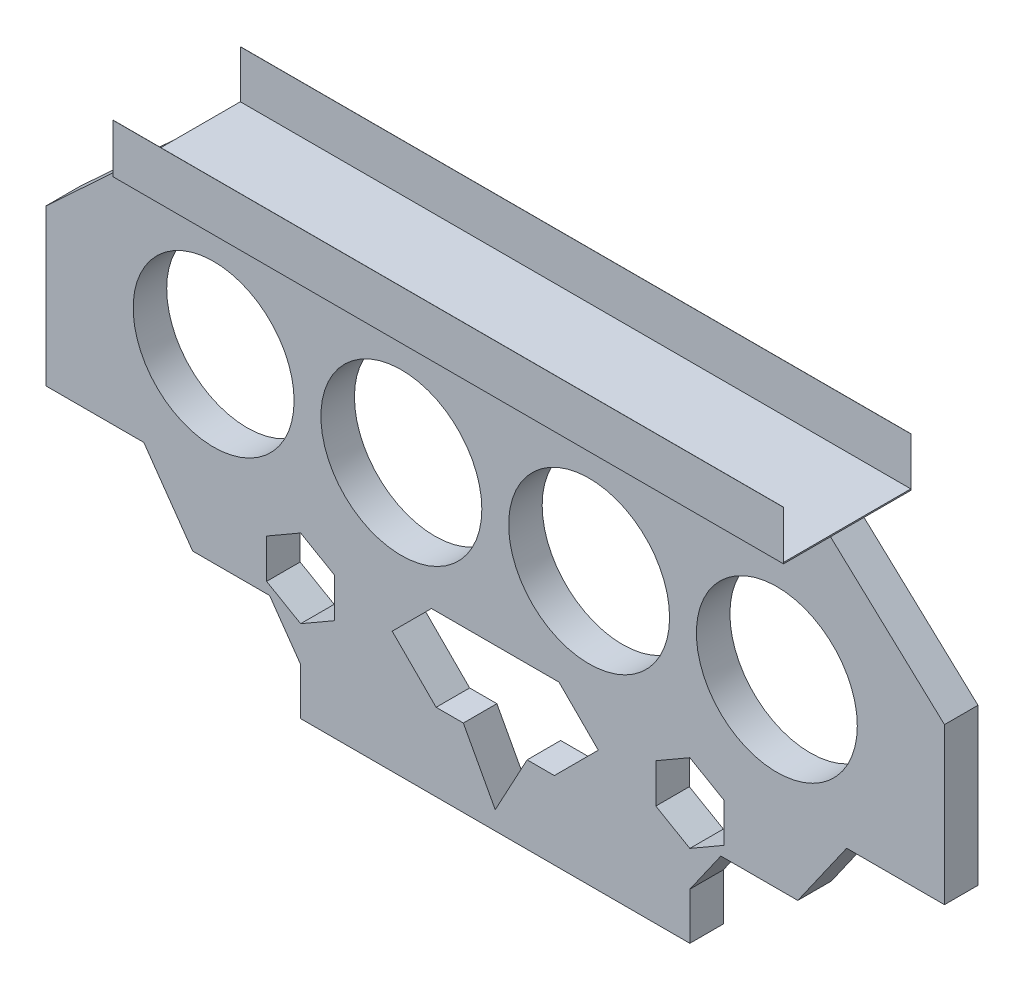
SolidWorks part; units mm, degrees
ref_plane "Front Plane" through (0, 0, 0) normal (0, 0, 1) x (1, 0, 0)
ref_plane "Top Plane" through (0, 0, 0) normal (0, 1, 0) x (1, 0, 0)
ref_plane "Right Plane" through (0, 0, 0) normal (1, 0, 0) x (0, 0, -1)
sketch "Sketch1" plane through (0, 0, 0) normal (0, 0, 1) x (1, 0, 0)
  line L1 (-67, -31.5) -> (67, -31.5)
  line L2 (-67, -31.5) -> (-67, 31.5)
  line L3 (-67, 31.5) -> (67, 31.5)
  line L4 (67, -31.5) -> (67, 31.5)
  line L5 (-67, -31.5) -> (67, 31.5) construction
  line L6 (-67, 31.5) -> (67, -31.5) construction
  point P0 (0, 0)
  dimension "D1" = 134
  dimension "D2" = 63
extrude "Boss-Extrude1" add sketch "Sketch1" against normal blind 5
sketch "Sketch3" plane through (0, 0, 0) normal (0, 0, 1) x (1, 0, 0)
  line L0 (-67, 31.5) -> (-67, -31.5) construction
  line L2 (67, -31.5) -> (67, 31.5) construction
  circle A0 centre (-42, 9.0713) radius 12
  circle A1 centre (-14, 9.0713) radius 12
  circle A2 centre (14, 9.0713) radius 12
  circle A3 centre (42, 9.0713) radius 12
  dimension "D1" = 28
  dimension "D2" = 25
  dimension "D3" = 28
  dimension "D4" = 28
  dimension "D5" = 25
extrude "Cut-Extrude1" cut sketch "Sketch3" against normal blind 10 contours A1 | A0 | A2 | A3
sketch "Sketch4" plane through (0, 0, 0) normal (0, 0, 1) x (1, 0, 0)
  line L0 (-67, -7.5206) -> (-52.4118, -7.5206)
  line L1 (-67, 31.5) -> (-67, -31.5) construction
  line L2 (-52.4118, -7.5206) -> (-45.1238, -17.91)
  line L3 (-45.1238, -17.91) -> (-33.649, -17.91)
  line L4 (-33.649, -17.91) -> (-29.0235, -24.5037)
  line L5 (-29.0235, -24.5037) -> (-29.0235, -31.5)
  line L6 (-67, -31.5) -> (67, -31.5) construction
  line L7 (-67, -7.5206) -> (-67, -31.5)
  line L8 (-67, -31.5) -> (-29.0235, -31.5)
  line L9 (0, 43.4956) -> (0, -7.5206) construction
  line L10 (67, -7.5206) -> (67, -31.5)
  line L11 (67, -7.5206) -> (52.4118, -7.5206)
  line L12 (52.4118, -7.5206) -> (45.1238, -17.91)
  line L13 (45.1238, -17.91) -> (33.649, -17.91)
  line L14 (33.649, -17.91) -> (29.0235, -24.5037)
  line L15 (29.0235, -24.5037) -> (29.0235, -31.5)
  line L16 (67, -31.5) -> (29.0235, -31.5)
  line L17 (-50, 31.5) -> (-67, 15.739)
  line L18 (67, 31.5) -> (-67, 31.5) construction
  line L19 (-67, 15.739) -> (-67, 31.5)
  line L20 (-67, 31.5) -> (-50, 31.5)
  line L21 (67, 15.739) -> (67, 31.5)
  line L22 (50, 31.5) -> (67, 15.739)
  line L23 (67, 31.5) -> (50, 31.5)
  line L24 (9.5114, -7.5206) -> (-9.5114, -7.5206)
  line L25 (-9.5114, -7.5206) -> (-15.37, -13.3792)
  line L26 (-15.37, -13.3792) -> (-8.816, -19.9332)
  line L27 (-8.816, -19.9332) -> (-4.7557, -19.9332)
  line L28 (-4.7557, -19.9332) -> (-2.2907, -24.5037)
  line L29 (-2.2907, -24.5037) -> (0, -28.751)
  line L31 (2.2907, -24.5037) -> (0, -28.751)
  line L32 (4.7557, -19.9332) -> (2.2907, -24.5037)
  line L33 (8.816, -19.9332) -> (4.7557, -19.9332)
  line L34 (15.37, -13.3792) -> (8.816, -19.9332)
  line L35 (9.5114, -7.5206) -> (15.37, -13.3792)
  line L36 (0, -28.751) -> (0, -47.0621) construction
  line L37 (-34.0972, -10.4499) -> (-29.0235, -7.5206)
  line L38 (29.0235, -7.5206) -> (23.9498, -10.4499)
  line L39 (23.9498, -10.4499) -> (23.9498, -16.3085)
  line L40 (23.9498, -16.3085) -> (29.0235, -19.2378)
  line L41 (29.0235, -19.2378) -> (34.0972, -16.3085)
  line L42 (34.0972, -16.3085) -> (34.0972, -10.4499)
  line L43 (34.0972, -10.4499) -> (29.0235, -7.5206)
  line L44 (-34.0972, -16.3085) -> (-34.0972, -10.4499)
  line L45 (-29.0235, -19.2378) -> (-34.0972, -16.3085)
  line L46 (-23.9498, -16.3085) -> (-29.0235, -19.2378)
  line L47 (-23.9498, -10.4499) -> (-23.9498, -16.3085)
  line L48 (-29.0235, -7.5206) -> (-23.9498, -10.4499)
  circle A0 centre (29.0235, -13.3792) radius 5.0737 construction
  dimension "D1" = 100
extrude "Cut-Extrude2" cut sketch "Sketch4" against normal blind 10
ref_plane "Plane1" through (50, 0, 0) normal (1, 0, 0) x (0, 0, -1)
sketch "Sketch5" plane through (50, 0, 0) normal (1, 0, 0) x (0, 0, -1)
  line L0 (5, 31.5) -> (12, 31.5)
  line L1 (12, 31.5) -> (12, 38.8042)
  line L2 (12, 38.8042) -> (11.9806, 38.8042)
  line L3 (11.9806, 38.8042) -> (11.9806, 31.6961)
  line L4 (11.9806, 31.6961) -> (5.9806, 31.6961)
  line L6 (2.5, 31.5) -> (2.5, 47.421) construction
  line L7 (5, 31.5) -> (0, 31.5) construction
  line L8 (-6.9806, 31.6961) -> (-0.9806, 31.6961)
  line L9 (-6.9806, 38.8042) -> (-6.9806, 31.6961)
  line L10 (-7, 38.8042) -> (-6.9806, 38.8042)
  line L11 (-7, 31.5) -> (-7, 38.8042)
  line L12 (0, 31.5) -> (-7, 31.5)
  line L13 (-0.9806, 31.6961) -> (5.9806, 31.6961)
  line L14 (0, 31.5) -> (5, 31.5)
  dimension "D1" = 7
  dimension "D2" = 6
  dimension "D3" = 1
extrude "Boss-Extrude2" add sketch "Sketch5" against normal blind 100
